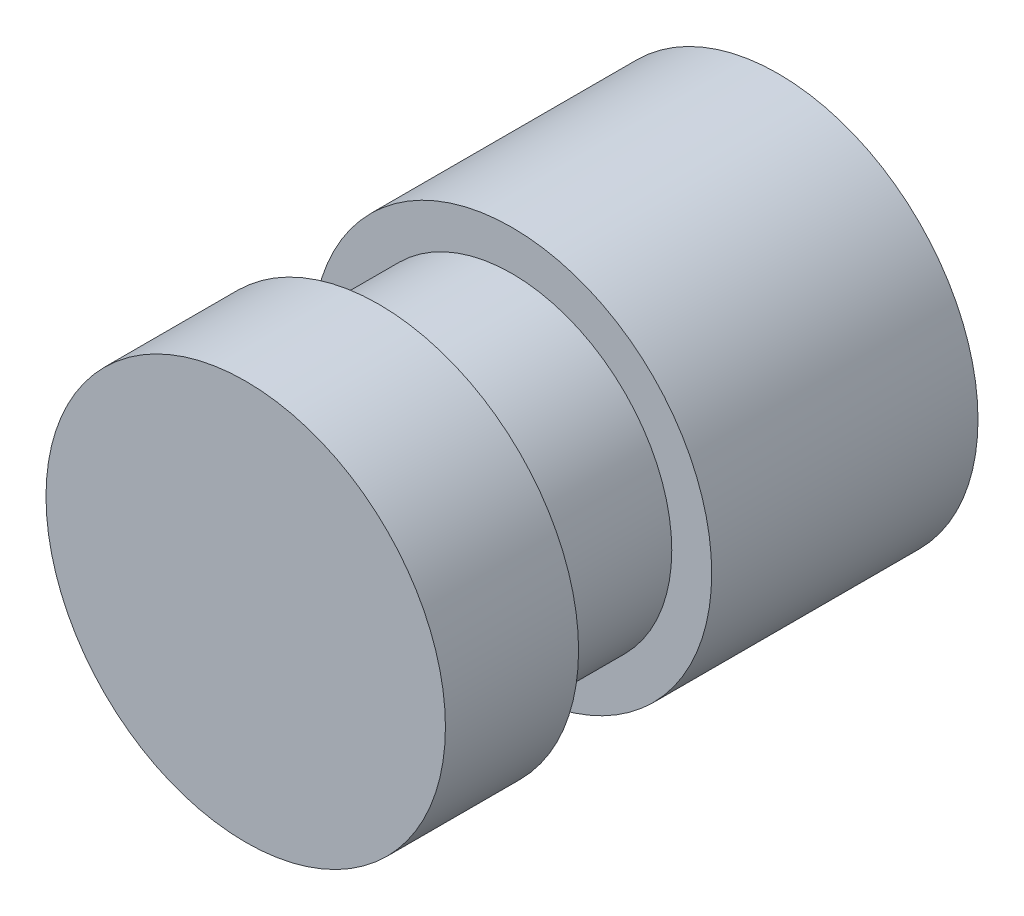
SolidWorks part; units mm, degrees
material "1060 Alloy"
ref_plane "Front Plane" through (0, 0, 0) normal (0, 0, 1) x (1, 0, 0)
ref_plane "Top Plane" through (0, 0, 0) normal (0, 1, 0) x (1, 0, 0)
ref_plane "Right Plane" through (0, 0, 0) normal (1, 0, 0) x (0, 0, -1)
sketch "Sketch1" plane through (0, 0, 0) normal (0, 0, 1) x (1, 0, 0)
  circle A0 centre (0, 0) radius 7.5
extrude "Boss-Extrude1" add sketch "Sketch1" against normal blind 20 contours A0
ref_plane "Plane1" through (0, 0, -7.5) normal (0, 0, 1) x (1, 0, 0)
sketch "Sketch4" plane through (0, 0, -7.5) normal (0, 0, 1) x (1, 0, 0)
  circle A0 centre (0, 0) radius 6
  circle A1 centre (0, 0) radius 7.5
extrude "Cut-Extrude2" cut sketch "Sketch4" against normal blind 2.5 and the other way blind 2.5
sketch "Sketch5" plane through (0, 0, -20) normal (0, 0, -1) x (-1, 0, 0)
  point P0 (0, 0)
